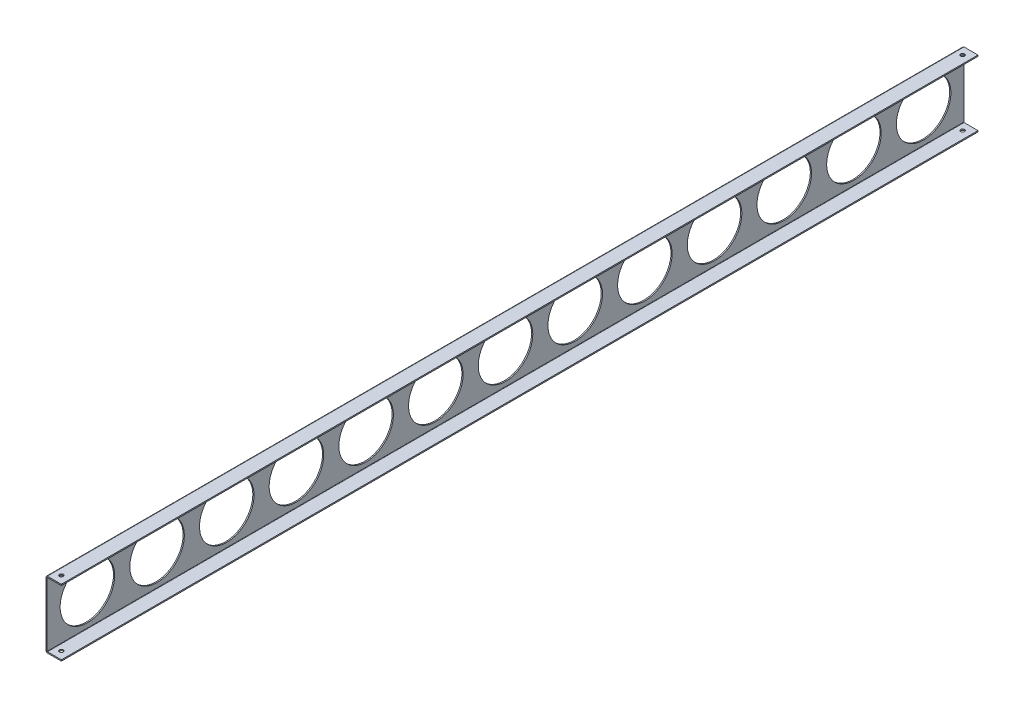
SolidWorks part; units mm, degrees
material "6061-T6 (SS)"
ref_plane "Front" through (0, 0, 0) normal (0, 0, 1) x (1, 0, 0)
ref_plane "Top" through (0, 0, 0) normal (0, 1, 0) x (1, 0, 0)
ref_plane "Right" through (0, 0, 0) normal (1, 0, 0) x (0, 0, -1)
sketch "Sketch1" plane through (0, 0, 0) normal (0, 0, 1) x (1, 0, 0)
  line L0 (0, 52.46) -> (0, -52.46)
  line L1 (0, 0) -> (72.936, 0) construction
  line L2 (2.54, 55) -> (25.4, 55)
  line L3 (2.54, -55) -> (25.4, -55)
  arc A0 (0, -52.46) -> (2.54, -55) centre (2.54, -52.46) ccw
  arc A1 (0, 52.46) -> (2.54, 55) centre (2.54, 52.46) cw
  point P9 (0, -76.2)
  dimension "D3" = 2.54
  dimension "D1" = 110
  dimension "D2" = 25.4
extrude "Extrude-Thin1" add sketch "Sketch1" along normal mid plane 1512.6192 thin thin type one direction reverse wall 2
sketch "Sketch2" plane through (2, 0, 0) normal (1, 0, 0) x (0, 0, -1)
  circle A0 centre (0, 0) radius 45
  dimension "D1" = 90
extrude "Extrude1" cut sketch "Sketch2" against normal through all
pattern_linear "LPattern1" count 7 spacing 115 along (0, 0, 1) of "Extrude1"
pattern_linear "LPattern2" count 7 spacing 115 along (0, 0, -1) of "Extrude1"
sketch "Sketch3" plane through (0, -55, 0) normal (0, -1, 0) x (1, 0, 0)
  line L0 (0, 756.3096) -> (0, -756.3096) construction
  line L1 (2.54, 756.3096) -> (25.4, 756.3096) construction
  line L2 (25.4, 756.3096) -> (25.4, -756.3096) construction
  circle A0 centre (12.7, 743.6096) radius 12.7 construction
  circle A1 centre (12.7, 743.6096) radius 3.175
  dimension "D1" = 6.35
extrude "Extrude2" cut sketch "Sketch3" against normal through all
mirror "Mirror1" about plane through (0, 0, 0) normal (0, 0, 1) of "Extrude2"
